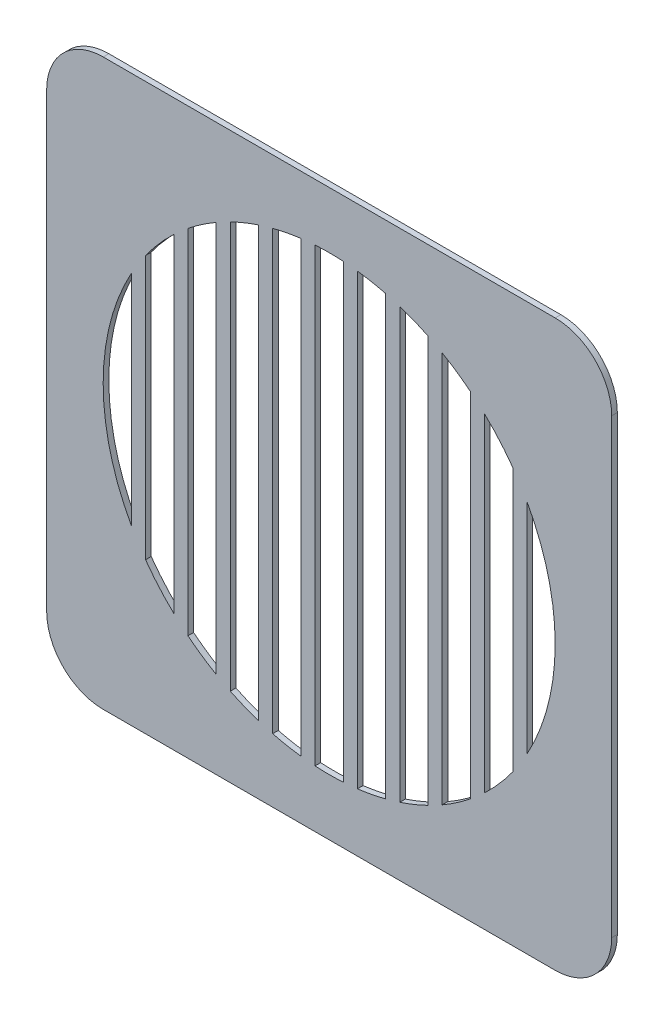
SolidWorks part; units mm, degrees
ref_plane "Front Plane" through (0, 0, 0) normal (0, 0, 1) x (1, 0, 0)
ref_plane "Top Plane" through (0, 0, 0) normal (0, 1, 0) x (1, 0, 0)
ref_plane "Right Plane" through (0, 0, 0) normal (1, 0, 0) x (0, 0, -1)
sketch "Sketch1" plane through (0, 0, 0) normal (0, 0, 1) x (1, 0, 0)
  line L0 (-50, 0) -> (50, 0) construction
  line L1 (-40, 50) -> (40, 50)
  line L2 (-50, 40) -> (-50, -40)
  line L3 (-40, -50) -> (40, -50)
  line L4 (50, 40) -> (50, -40)
  line L5 (0, 50) -> (0, -50) construction
  arc A0 (40, -50) -> (50, -40) centre (40, -40) ccw
  arc A1 (-50, -40) -> (-40, -50) centre (-40, -40) ccw
  arc A2 (40, 50) -> (50, 40) centre (40, 40) cw
  arc A3 (-40, 50) -> (-50, 40) centre (-40, 40) ccw
  circle A8 centre (0, 0) radius 40
  dimension "D3" = 10
  dimension "D4" = 80
  dimension "D1" = 100
  dimension "D2" = 100
extrude "Boss-Extrude1" add sketch "Sketch1" along normal blind 1
sketch "Sketch3" plane through (0, 0, 1) normal (0, 0, 1) x (1, 0, 0)
  line L1 (-35, 40) -> (-32.5, 40)
  line L2 (-35, 40) -> (-35, -40)
  line L3 (-35, -40) -> (-32.5, -40)
  line L4 (-32.5, 40) -> (-32.5, -40)
  line L7 (-27.5, 40) -> (-27.5, -40)
  line L8 (-27.5, 40) -> (-25, 40)
  line L9 (-25, 40) -> (-25, -40)
  line L10 (-27.5, -40) -> (-25, -40)
  line L11 (-20, 40) -> (-20, -40)
  line L12 (-20, 40) -> (-17.5, 40)
  line L13 (-17.5, 40) -> (-17.5, -40)
  line L14 (-20, -40) -> (-17.5, -40)
  line L15 (-12.5, 40) -> (-12.5, -40)
  line L16 (-12.5, 40) -> (-10, 40)
  line L17 (-10, 40) -> (-10, -40)
  line L18 (-12.5, -40) -> (-10, -40)
  line L19 (-5, 40) -> (-5, -40)
  line L20 (-5, 40) -> (-2.5, 40)
  line L21 (-2.5, 40) -> (-2.5, -40)
  line L22 (-5, -40) -> (-2.5, -40)
  line L23 (2.5, 40) -> (2.5, -40)
  line L24 (2.5, 40) -> (5, 40)
  line L25 (5, 40) -> (5, -40)
  line L26 (2.5, -40) -> (5, -40)
  line L27 (10, 40) -> (10, -40)
  line L28 (10, 40) -> (12.5, 40)
  line L29 (12.5, 40) -> (12.5, -40)
  line L30 (10, -40) -> (12.5, -40)
  line L31 (17.5, 40) -> (17.5, -40)
  line L32 (17.5, 40) -> (20, 40)
  line L33 (20, 40) -> (20, -40)
  line L34 (17.5, -40) -> (20, -40)
  line L35 (25, 40) -> (25, -40)
  line L36 (25, 40) -> (27.5, 40)
  line L37 (27.5, 40) -> (27.5, -40)
  line L38 (25, -40) -> (27.5, -40)
  line L39 (32.5, 40) -> (32.5, -40)
  line L40 (32.5, 40) -> (35, 40)
  line L41 (35, 40) -> (35, -40)
  line L42 (32.5, -40) -> (35, -40)
  line L43 (40, 50) -> (-40, 50) construction
  dimension "D1" = 10
  dimension "D2" = 2.5
  dimension "D3" = 80
  dimension "D4" = 10
extrude "Boss-Extrude2" add sketch "Sketch3" against normal blind 1
